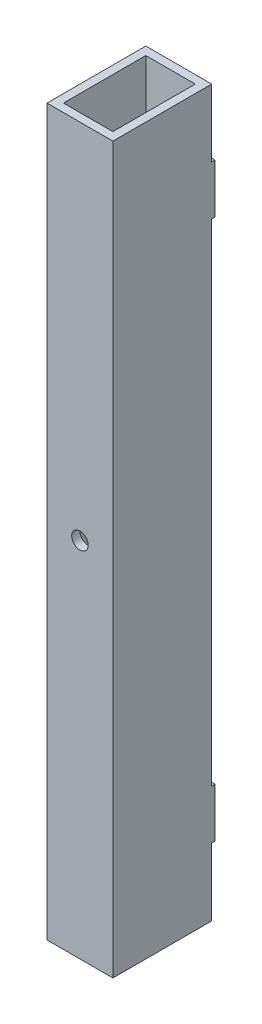
SolidWorks part; units mm, degrees
material "Plain Carbon Steel"
ref_plane "Front Plane" through (0, 0, 0) normal (0, 0, 1) x (1, 0, 0)
ref_plane "Top Plane" through (0, 0, 0) normal (0, 1, 0) x (1, 0, 0)
ref_plane "Right Plane" through (0, 0, 0) normal (1, 0, 0) x (0, 0, -1)
sketch "Sketch1" plane through (0, 0, 0) normal (0, 1, 0) x (1, 0, 0)
  line L1 (-25.4, -38.1) -> (25.4, -38.1)
  line L2 (-25.4, -38.1) -> (-25.4, 38.1)
  line L3 (-25.4, 38.1) -> (25.4, 38.1)
  line L4 (25.4, -38.1) -> (25.4, 38.1)
  line L5 (-25.4, -38.1) -> (25.4, 38.1) construction
  line L6 (-25.4, 38.1) -> (25.4, -38.1) construction
  line L7 (-19.05, -31.75) -> (19.05, -31.75)
  line L8 (-19.05, -31.75) -> (-19.05, 31.75)
  line L9 (-19.05, 31.75) -> (19.05, 31.75)
  line L10 (19.05, -31.75) -> (19.05, 31.75)
  line L11 (-19.05, -31.75) -> (19.05, 31.75) construction
  line L12 (-19.05, 31.75) -> (19.05, -31.75) construction
  point P0 (0, 0)
  point P6 (0, 0)
  dimension "D1" = 6.35
  dimension "D2" = 6.35
  dimension "D3" = 50.8
  dimension "D4" = 76.2
extrude "Boss-Extrude1" add sketch "Sketch1" along normal mid plane 558.8
sketch "Sketch2" plane through (0, 0, 38.1) normal (0, 0, 1) x (1, 0, 0)
  circle A0 centre (0, 0) radius 6.35
  dimension "D1" = 12.7
extrude "Cut-Extrude1" cut sketch "Sketch2" against normal through all
sketch "Sketch3" plane through (0, 0, -38.1) normal (0, 0, -1) x (-1, 0, 0)
  line L0 (-25.4, 279.4) -> (-25.4, -279.4) construction
  line L1 (-25.4, -227.4361) -> (25.4, -227.4361)
  line L2 (-25.4, -227.4361) -> (-25.4, -189.3361)
  line L3 (-25.4, -189.3361) -> (25.4, -189.3361)
  line L4 (25.4, -227.4361) -> (25.4, -189.3361)
  line L5 (25.4, 279.4) -> (25.4, -279.4) construction
  dimension "D1" = 38.1
extrude "Boss-Extrude2" add sketch "Sketch3" along normal blind 2.54
mirror "Mirror1" about plane through (0, 0, 0) normal (0, 1, 0) of "Boss-Extrude2"
equation "\"D2@Sketch1\" = \"D1@Sketch1\""
